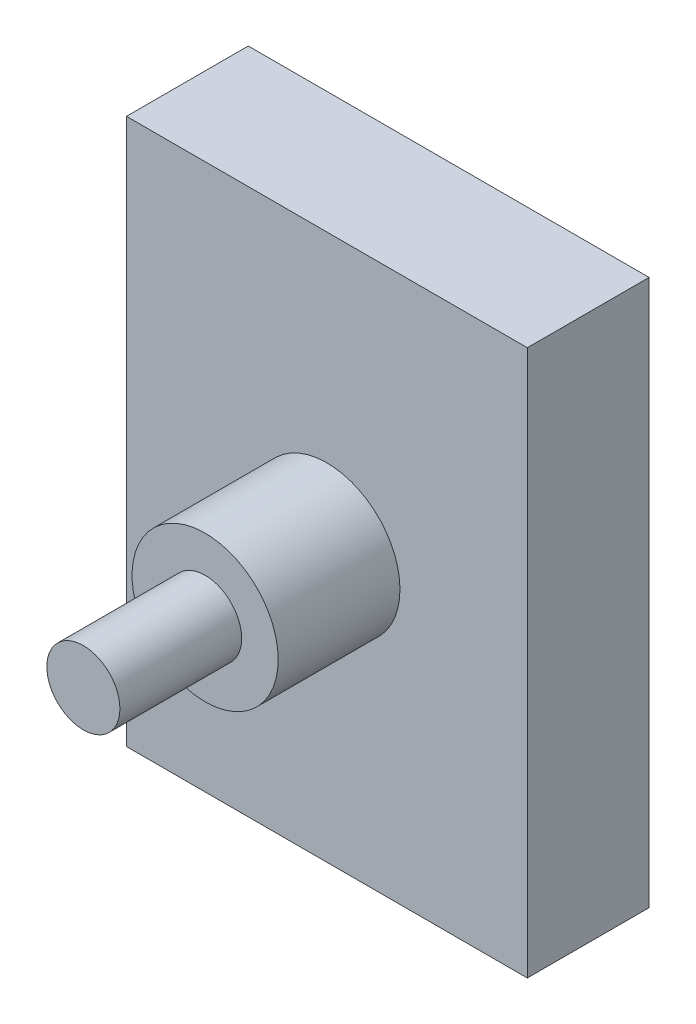
SolidWorks part; units mm, degrees
material "ABS"
ref_plane "Front Plane" through (0, 0, 0) normal (0, 0, 1) x (1, 0, 0)
ref_plane "Top Plane" through (0, 0, 0) normal (0, 1, 0) x (1, 0, 0)
ref_plane "Right Plane" through (0, 0, 0) normal (1, 0, 0) x (0, 0, -1)
sketch "Sketch2" plane through (0, 0, 0) normal (0, 0, 1) x (1, 0, 0)
  line L1 (-16.4593, -22.4131) -> (16.4593, -22.4131)
  line L2 (-16.4593, -22.4131) -> (-16.4593, 22.4131)
  line L3 (-16.4593, 22.4131) -> (16.4593, 22.4131)
  line L4 (16.4593, -22.4131) -> (16.4593, 22.4131)
  line L5 (-16.4593, -22.4131) -> (16.4593, 22.4131) construction
  line L6 (-16.4593, 22.4131) -> (16.4593, -22.4131) construction
  point P0 (0, 0)
extrude "Boss-Extrude1" add sketch "Sketch2" along normal blind 10
sketch "Sketch3" plane through (0, 0, 10) normal (0, 0, 1) x (1, 0, 0)
  circle A0 centre (0, 0) radius 6
extrude "Boss-Extrude2" add sketch "Sketch3" along normal blind 10
sketch "Sketch4" plane through (0, 0, 20) normal (0, 0, 1) x (1, 0, 0)
  circle A0 centre (0, 0) radius 3
extrude "Boss-Extrude3" add sketch "Sketch4" along normal blind 10
